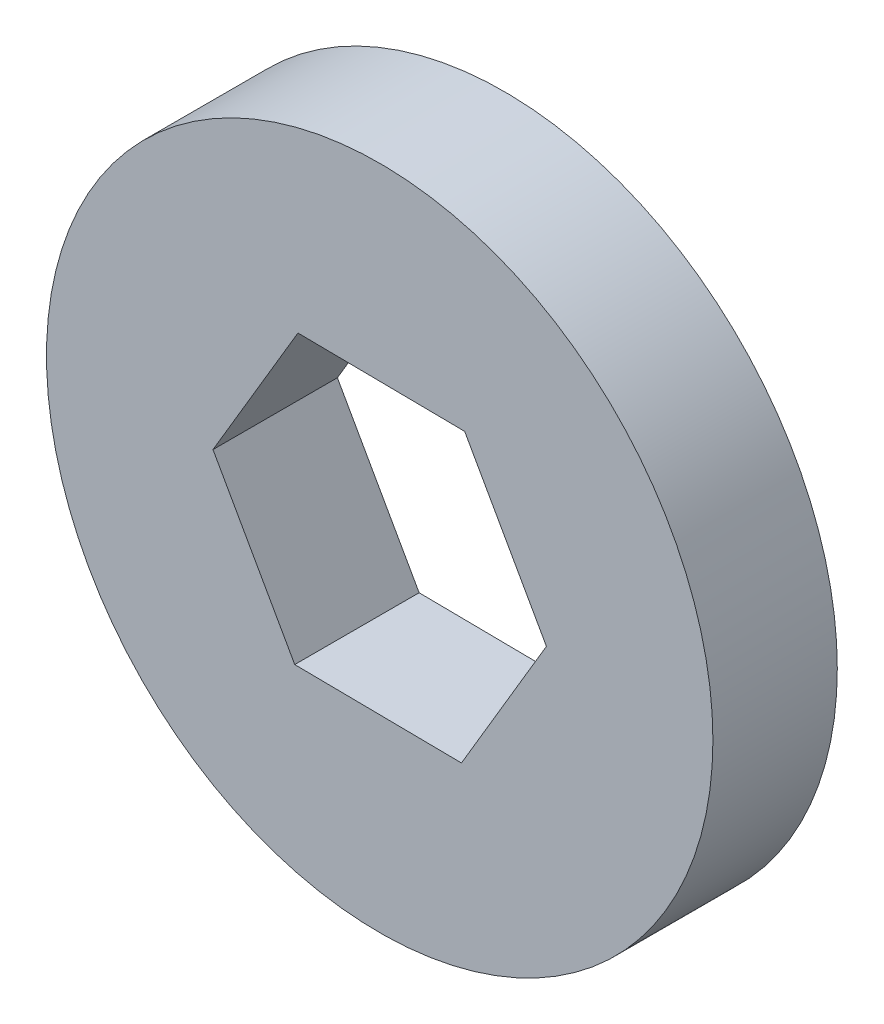
SolidWorks part; units mm, degrees
ref_plane "Alzado" through (0, 0, 0) normal (0, 0, 1) x (1, 0, 0)
ref_plane "Planta" through (0, 0, 0) normal (0, 1, 0) x (1, 0, 0)
ref_plane "Vista lateral" through (0, 0, 0) normal (1, 0, 0) x (0, 0, -1)
sketch "Croquis1" plane through (0, 0, 0) normal (0, 0, 1) x (1, 0, 0)
  line L1 (3.68, -6.5415) -> (7.5051, -0.0838)
  line L2 (7.5051, -0.0838) -> (3.8251, 6.4577)
  line L3 (3.8251, 6.4577) -> (-3.68, 6.5415)
  line L4 (-3.68, 6.5415) -> (-7.5051, 0.0838)
  line L5 (-7.5051, 0.0838) -> (-3.8251, -6.4577)
  line L6 (-3.8251, -6.4577) -> (3.68, -6.5415)
  circle A0 centre (0, 0) radius 6.5 construction
  circle A1 centre (0, 0) radius 15
  dimension "D2" = 30
  dimension "D1" = 13
extrude "Saliente-Extruir1" add sketch "Croquis1" along normal blind 5.6
